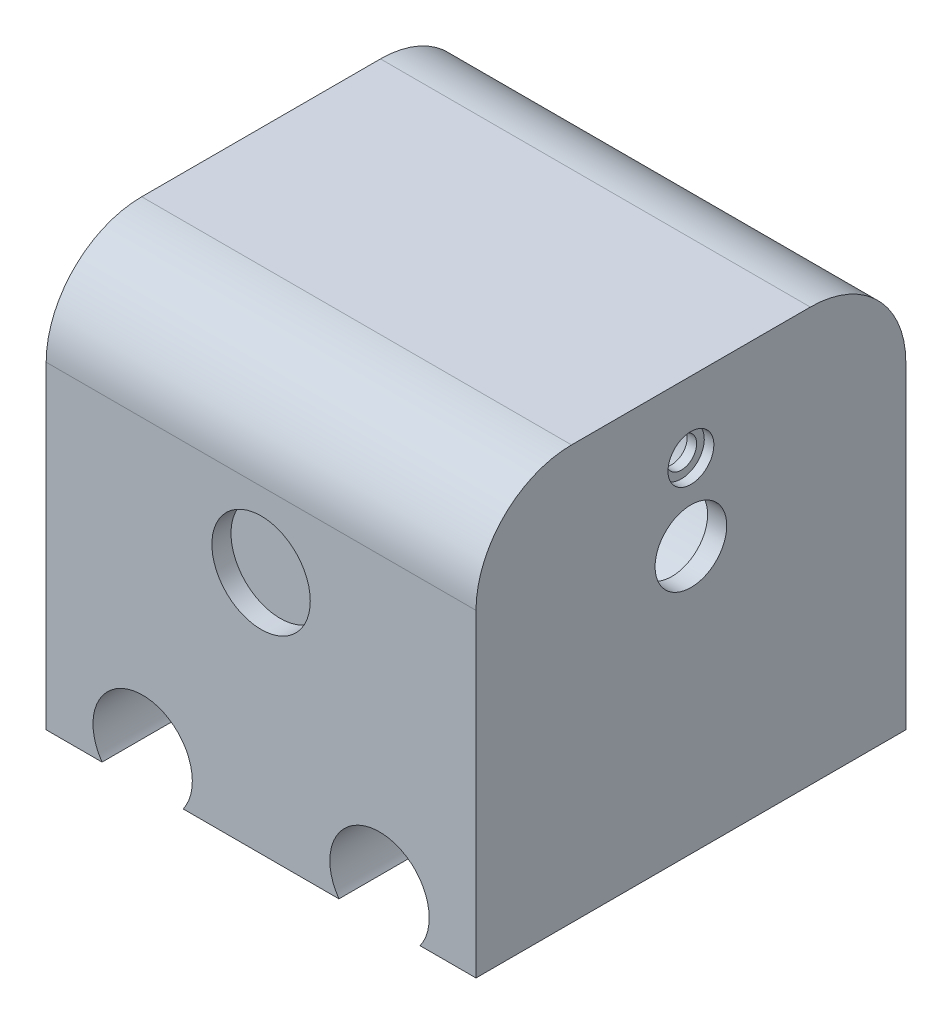
SolidWorks part; units mm, degrees
ref_plane "Front Plane" through (0, 0, 0) normal (0, 0, 1) x (1, 0, 0)
ref_plane "Top Plane" through (0, 0, 0) normal (0, 1, 0) x (1, 0, 0)
ref_plane "Right Plane" through (0, 0, 0) normal (1, 0, 0) x (0, 0, -1)
sketch "Sketch1" plane through (0, 0, 0) normal (0, 0, 1) x (1, 0, 0)
  line L1 (-14.2634, 22.0982) -> (30.7366, 22.0982)
  line L2 (-14.2634, 22.0982) -> (-14.2634, -27.9018)
  line L3 (-14.2634, -27.9018) -> (30.7366, -27.9018)
  line L4 (30.7366, 22.0982) -> (30.7366, -27.9018)
  dimension "D1" = 50
  dimension "D2" = 45
extrude "Boss-Extrude1" add sketch "Sketch1" along normal blind 45
sketch "Sketch2" plane through (0, 0, 45) normal (0, 0, 1) x (1, 0, 0)
  line L0 (-14.2634, -27.9018) -> (30.7366, -27.9018) construction
  line L1 (-14.2634, 22.0982) -> (-14.2634, -27.9018) construction
  circle A0 centre (-4.1634, -24.9018) radius 5.2
  circle A1 centre (20.6366, -24.9018) radius 5.2
  dimension "D1" = 3
  dimension "D3" = 10.1
  dimension "D2" = 2
extrude "Cut-Extrude1" cut sketch "Sketch2" against normal blind 45
sketch "Sketch9" plane through (0, 0, 45) normal (0, 0, 1) x (1, 0, 0)
  line L0 (8.2366, 22.0982) -> (8.2366, -2.4018) construction
  line L1 (30.7366, 22.0982) -> (-14.2634, 22.0982) construction
  circle A0 centre (8.2366, -2.4018) radius 5.15
  dimension "D1" = 24.5
extrude "Cut-Extrude6" cut sketch "Sketch9" against normal blind 2
sketch "Sketch10" plane through (0, 0, 0) normal (0, 0, -1) x (-1, 0, 0)
  line L0 (-8.2366, 22.0982) -> (-8.2366, -2.4018) construction
  line L1 (-30.7366, 22.0982) -> (14.2634, 22.0982) construction
  circle A0 centre (-8.2366, -2.4018) radius 5.15
  dimension "D1" = 24.5
extrude "Cut-Extrude7" cut sketch "Sketch10" against normal blind 2
sketch "Sketch12" plane through (-14.2634, 0, 0) normal (-1, 0, 0) x (0, 0, 1)
  line L0 (22.5, 22.0982) -> (22.5, -7.2504) construction
  line L1 (45, 22.0982) -> (0, 22.0982) construction
  line L2 (0, -16.4263) -> (45, -16.4263) construction
  line L3 (0, 22.0982) -> (0, -27.9018) construction
  line L4 (45, 22.0982) -> (45, -27.9018) construction
  circle A0 centre (22.5, 0) radius 12.7
  dimension "D1" = 25.4
extrude "Cut-Extrude8" cut sketch "Sketch12" against normal blind 46
sketch "Sketch13" plane through (-14.2634, 0, 0) normal (-1, 0, 0) x (0, 0, 1)
  line L0 (45, 22.0982) -> (45, -27.9018) construction
  line L1 (0, 22.0982) -> (45, 22.0982)
  line L2 (0, 22.0982) -> (0, 15.4307)
  line L3 (0, 15.4307) -> (45, 15.4307)
  line L4 (45, 22.0982) -> (45, 15.4307)
extrude "Cut-Extrude9" cut sketch "Sketch13" against normal blind 46
sketch "Sketch16" plane through (30.7366, 0, 0) normal (1, 0, 0) x (0, 0, -1)
  circle A0 centre (-22.5, 0) radius 13.25
  circle A1 centre (-22.5, 0) radius 3.75
extrude "Boss-Extrude3" add sketch "Sketch16" against normal blind 2
fillet "Fillet1" radius 10 2 edges at (8.2366, 15.4307, 0) (8.2366, 15.4307, 45)
sketch "Sketch17" plane through (30.7366, 0, 0) normal (1, 0, 0) x (0, 0, -1)
  line L0 (-22.5, 0) -> (-22.5, 8) construction
  circle A0 centre (-22.5, 8) radius 1.6
  dimension "D1" = 8
extrude "Cut-Extrude10" cut sketch "Sketch17" against normal blind 10
sketch "Sketch18" plane through (30.7366, 0, 0) normal (1, 0, 0) x (0, 0, -1)
  line L0 (-22.5, 9.6) -> (-22.5, 8) construction
  circle A0 centre (-22.5, 8) radius 1.6 construction
  circle A1 centre (-22.5, 8) radius 2.4
extrude "Cut-Extrude11" cut sketch "Sketch18" against normal blind 1
